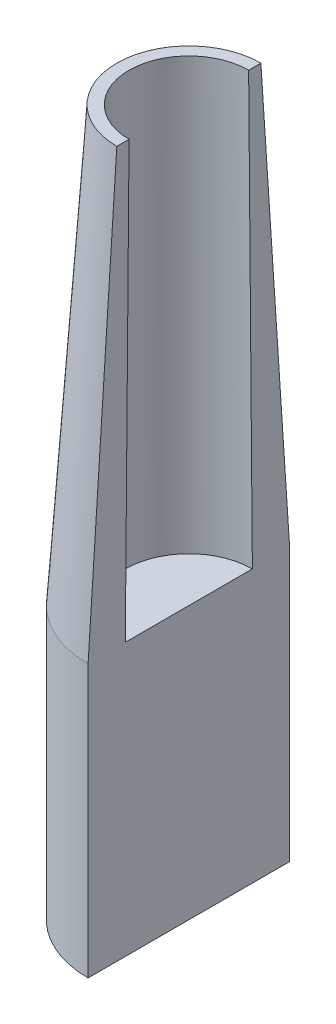
SolidWorks part; units mm, degrees
ref_plane "Front Plane" through (0, 0, 0) normal (0, 0, 1) x (1, 0, 0)
ref_plane "Top Plane" through (0, 0, 0) normal (0, 1, 0) x (1, 0, 0)
ref_plane "Right Plane" through (0, 0, 0) normal (1, 0, 0) x (0, 0, -1)
sketch "Sketch2" plane through (0, 0, 0) normal (0, 1, 0) x (1, 0, 0)
  circle A0 centre (0, 0) radius 25.4
extrude "Boss-Extrude1" add sketch "Sketch2" along normal blind 63.5 and the other way blind 5.08 contours A0
sketch "Sketch3" plane through (0, 63.5, 0) normal (0, 1, 0) x (1, 0, 0)
  circle A0 centre (0, 0) radius 25.4
extrude "Boss-Extrude2" add sketch "Sketch3" along normal blind 109.3175 draft 3.793
sketch "Sketch4" plane through (0, 172.8175, 0) normal (0, 1, 0) x (1, 0, 0)
  circle A0 centre (0, 0) radius 15.0686
extrude "Cut-Extrude1" cut sketch "Sketch4" against normal blind 109.3175 draft 0.493 contours A0 draft outward yes
sketch "Sketch5" plane through (0, 0, 0) normal (0, 1, 0) x (1, 0, 0)
  line L0 (0, 25.4) -> (0, -25.4)
  circle A0 centre (0, 0) radius 25.4 construction
split "Split2" trim tools "Sketch5" bodies to split 103 resulting bodies 105
